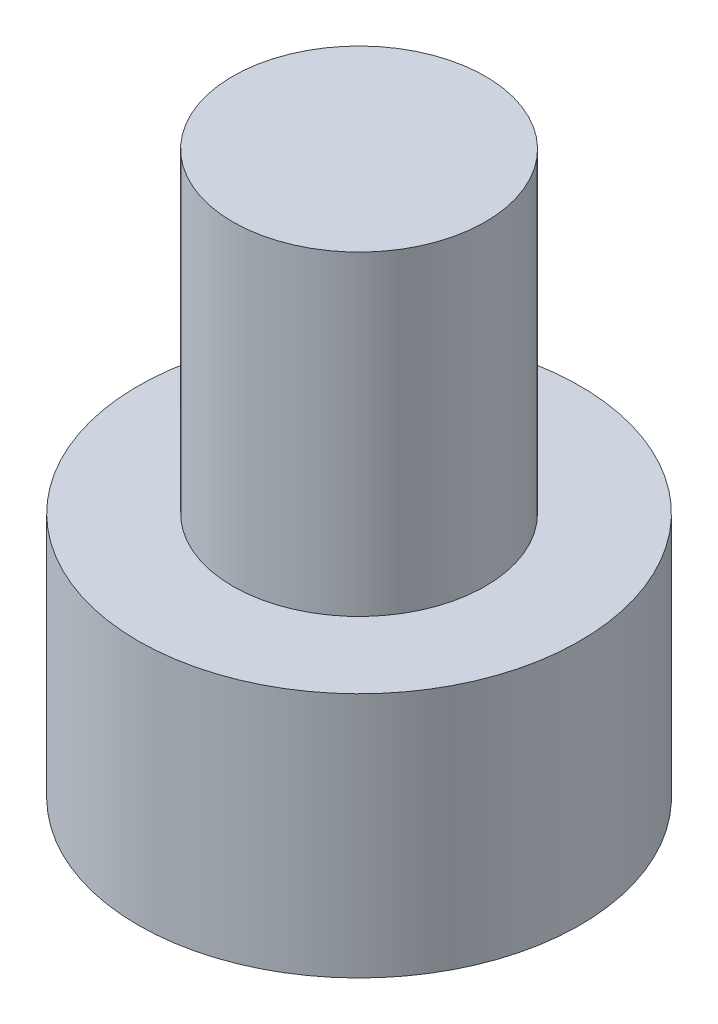
SolidWorks part; units mm, degrees
ref_plane "前视基准面" through (0, 0, 0) normal (0, 0, 1) x (1, 0, 0)
ref_plane "上视基准面" through (0, 0, 0) normal (0, 1, 0) x (1, 0, 0)
ref_plane "右视基准面" through (0, 0, 0) normal (1, 0, 0) x (0, 0, -1)
sketch "草图1" plane through (0, 0, 0) normal (0, 1, 0) x (1, 0, 0)
  circle A0 centre (0, 0) radius 3.5
extrude "凸台-拉伸1" add sketch "草图1" along normal blind 3.9
sketch "草图2" plane through (0, 3.9, 0) normal (0, 1, 0) x (1, 0, 0)
  circle A0 centre (0, 0) radius 2
extrude "凸台-拉伸2" add sketch "草图2" along normal blind 5
sketch "草图3" plane through (0, 0, 0) normal (0, -1, 0) x (1, 0, 0)
  line L1 (1.725, 0) -> (0.8625, 1.4939)
  line L2 (0.8625, 1.4939) -> (-0.8625, 1.4939)
  line L3 (-0.8625, 1.4939) -> (-1.725, 0)
  line L4 (-1.725, 0) -> (-0.8625, -1.4939)
  line L5 (-0.8625, -1.4939) -> (0.8625, -1.4939)
  line L6 (0.8625, -1.4939) -> (1.725, 0)
  circle A0 centre (0, 0) radius 1.4939 construction
extrude "切除-拉伸1" cut sketch "草图3" against normal blind 2.4
